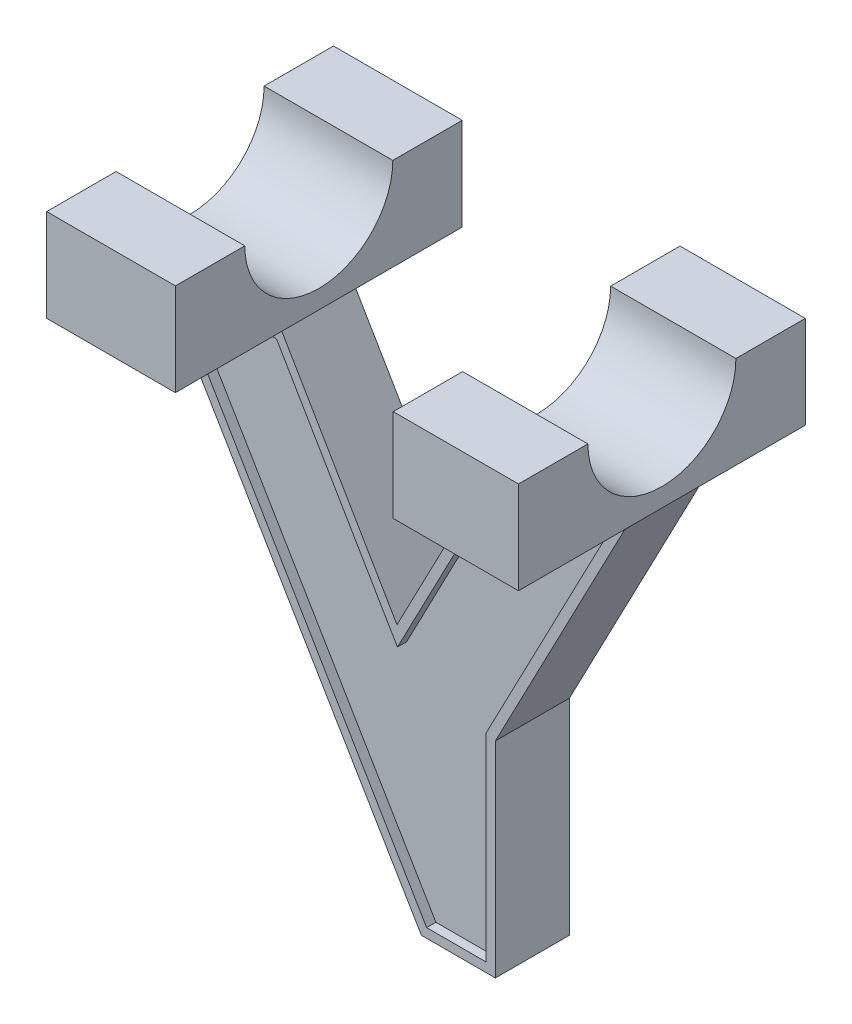
SolidWorks part; units mm, degrees
material "Калифорния"
ref_plane "Спереди" through (0, 0, 0) normal (0, 0, 1) x (1, 0, 0)
ref_plane "Сверху" through (0, 0, 0) normal (0, 1, 0) x (1, 0, 0)
ref_plane "Справа" through (0, 0, 0) normal (1, 0, 0) x (0, 0, -1)
sketch "Эскиз1" plane through (0, 0, 0) normal (0, 1, 0) x (1, 0, 0)
  line L1 (-25.5, 15.5) -> (25.5, 15.5)
  line L2 (-25.5, 15.5) -> (-25.5, -15.5)
  line L3 (-25.5, -15.5) -> (25.5, -15.5)
  line L4 (25.5, 15.5) -> (25.5, -15.5)
  line L5 (-25.5, 15.5) -> (25.5, -15.5) construction
  line L6 (-25.5, -15.5) -> (25.5, 15.5) construction
  point P0 (0, 0)
  dimension "D1" = 51
  dimension "D2" = 31
extrude "Бобышка-Вытянуть1" add sketch "Эскиз1" along normal blind 10
sketch "Эскиз2" plane through (25.5, 0, 0) normal (1, 0, 0) x (0, 0, -1)
  line L0 (-15.5, 10) -> (15.5, 10) construction
  circle A0 centre (0, 10) radius 8
extrude "Вырез-Вытянуть1" cut sketch "Эскиз2" against normal blind 51
sketch "Эскиз3" plane through (0, 0, 0) normal (0, -1, 0) x (1, 0, 0)
  line L0 (25.5, 15.5) -> (25.5, -15.5) construction
  line L1 (-25.5, 4) -> (25.5, 4)
  line L2 (-25.5, 4) -> (-25.5, -4)
  line L3 (-25.5, -4) -> (25.5, -4)
  line L4 (25.5, 4) -> (25.5, -4)
  line L5 (-25.5, 4) -> (25.5, -4) construction
  line L6 (-25.5, -4) -> (25.5, 4) construction
  point P0 (0, 0)
extrude "Бобышка-Вытянуть3" add sketch "Эскиз3" along normal blind 49
sketch "Эскиз4" plane through (0, 0, -4) normal (0, 0, -1) x (-1, 0, 0)
  line L0 (-25.5, 0) -> (-11.9592, 0)
  line L1 (25.5, -49) -> (25.5, 0) construction
  line L2 (-0.8636, -21.2471) -> (11.5876, 0)
  line L3 (-25.5, 0) -> (-11.5, -26.8028)
  line L4 (-25.5, -49) -> (-25.5, 0) construction
  line L5 (25.5, 0) -> (-25.5, 0) construction
  line L6 (-11.5, -49) -> (-11.5, -26.8028)
  line L7 (-11.9592, 0) -> (-0.8636, -21.2471)
  line L8 (25.5, -49) -> (-25.5, -49) construction
  line L9 (-11.5, -49) -> (-3.5, -49)
  line L10 (-3.5, -49) -> (25.5, 0)
  line L11 (-3.5, -49) -> (25.5, -49)
  line L12 (11.5876, 0) -> (25.5, 0)
  line L13 (25.5, -49) -> (25.5, 0)
  line L14 (-11.9592, 0) -> (11.5876, 0)
  line L15 (-25.5, -49) -> (-25.5, 0)
  line M1 (25.5, 0) -> (-25.5, 0)
  line M2 (-25.5, 0) -> (-25.5, -49)
  line M3 (-25.5, -49) -> (25.5, -49)
  line M4 (25.5, -49) -> (25.5, 0)
extrude "Вырез-Вытянуть4" cut sketch "Эскиз4" against normal blind 49 contours L10 M3 M4 | L6 L3 M3 M2 | L7 L2 M1
sketch "Эскиз6" plane through (0, 0, 0) normal (0, -1, 0) x (-1, 0, 0)
  line L0 (11.5876, 4) -> (11.5876, -15.5)
  line L1 (25.5, -15.5) -> (-25.5, -15.5) construction
  line L2 (11.5876, 4) -> (11.5876, 15.5)
  line L3 (-25.5, 15.5) -> (25.5, 15.5) construction
  line L4 (-11.9592, 4) -> (-11.9592, 15.5)
  line L5 (-11.9592, -4) -> (-11.9592, -15.5)
  line L7 (-11.9592, 4) -> (-11.9592, -4)
  line L8 (-11.9592, 15.5) -> (11.5876, 15.5)
  line L9 (11.5876, -15.5) -> (-11.9592, -15.5)
extrude "Вырез-Вытянуть5" cut sketch "Эскиз6" against normal blind 49
sketch "Эскиз7" plane through (0, 0, -4) normal (0, 0, -1) x (-1, 0, 0)
  line L16 (23.7462, -1) -> (12.1606, -1)
  line L17 (12.1606, -1) -> (-0.914, -23.3109)
  line L18 (-0.914, -23.3109) -> (-12.5651, -1)
  line L19 (-12.5651, -1) -> (-23.8495, -1)
  line L20 (-23.8495, -1) -> (-10.5, -26.5574)
  line L21 (-10.5, -26.5574) -> (-10.5, -48)
  line L22 (-10.5, -48) -> (-4.0702, -48)
  line L23 (-4.0702, -48) -> (23.7462, -1)
  line L24 (23.7462, -1) -> (12.1606, -1)
  line L25 (12.1606, -1) -> (-0.914, -23.3109)
  line L26 (-0.914, -23.3109) -> (-12.5651, -1)
  line L27 (-12.5651, -1) -> (-23.8495, -1)
  line L28 (-23.8495, -1) -> (-10.5, -26.5574)
  line L29 (-10.5, -26.5574) -> (-10.5, -48)
  line L30 (-10.5, -48) -> (-4.0702, -48)
  line L31 (-4.0702, -48) -> (23.7462, -1)
  dimension "D1" = 1
extrude "Вырез-Вытянуть6" cut sketch "Эскиз7" against normal blind 1
sketch "Эскиз8" plane through (0, 0, 4) normal (0, 0, 1) x (1, 0, 0)
  line L16 (12.5651, -1) -> (0.914, -23.3109)
  line L17 (0.914, -23.3109) -> (-12.1606, -1)
  line L18 (-12.1606, -1) -> (-23.7462, -1)
  line L19 (-23.7462, -1) -> (4.0702, -48)
  line L20 (4.0702, -48) -> (10.5, -48)
  line L21 (10.5, -48) -> (10.5, -26.5574)
  line L22 (10.5, -26.5574) -> (23.8495, -1)
  line L23 (23.8495, -1) -> (12.5651, -1)
  line L24 (12.5651, -1) -> (0.914, -23.3109)
  line L25 (0.914, -23.3109) -> (-12.1606, -1)
  line L26 (-12.1606, -1) -> (-23.7462, -1)
  line L27 (-23.7462, -1) -> (4.0702, -48)
  line L28 (4.0702, -48) -> (10.5, -48)
  line L29 (10.5, -48) -> (10.5, -26.5574)
  line L30 (10.5, -26.5574) -> (23.8495, -1)
  line L31 (23.8495, -1) -> (12.5651, -1)
  dimension "D1" = 1
extrude "Вырез-Вытянуть7" cut sketch "Эскиз8" against normal blind 1
